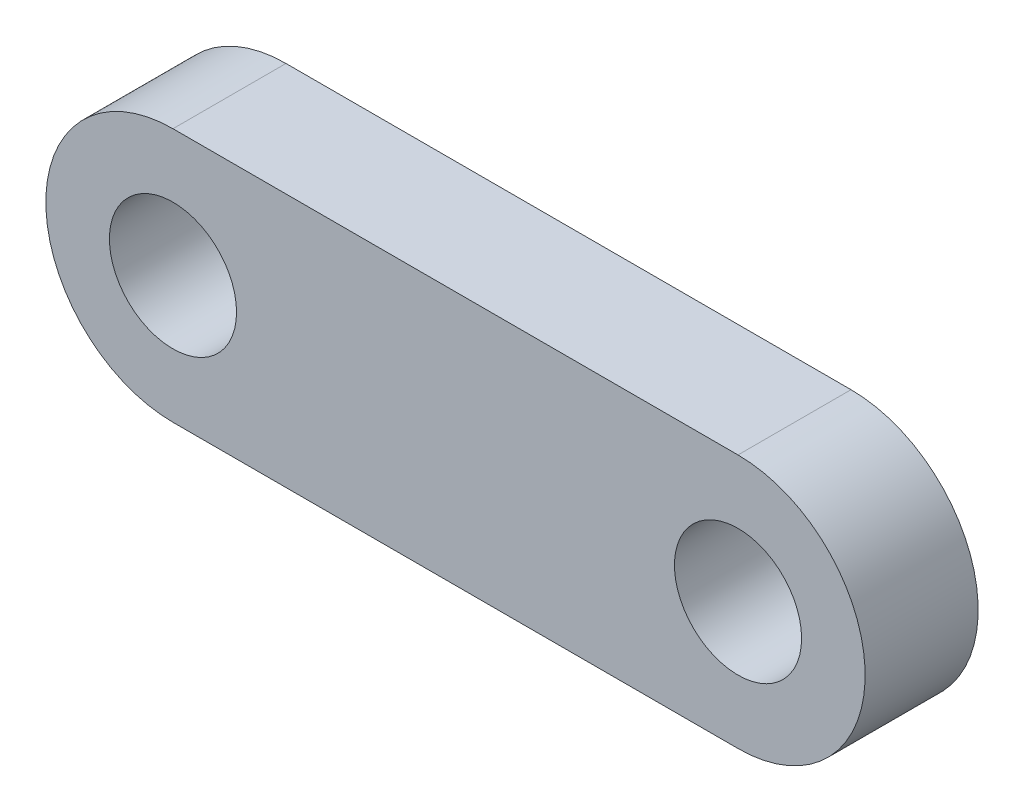
SolidWorks part; units mm, degrees
ref_plane "Front Plane" through (0, 0, 0) normal (0, 0, 1) x (1, 0, 0)
ref_plane "Top Plane" through (0, 0, 0) normal (0, 1, 0) x (1, 0, 0)
ref_plane "Right Plane" through (0, 0, 0) normal (1, 0, 0) x (0, 0, -1)
sketch "Sketch1" plane through (0, 0, 0) normal (0, 0, 1) x (1, 0, 0)
  line L0 (-10, 4.5) -> (10, 4.5)
  line L1 (10, -4.5) -> (-10, -4.5)
  circle A0 centre (-10, 0) radius 4.5
  circle A1 centre (10, 0) radius 4.5
  circle A2 centre (-10, 0) radius 2.25
  circle A3 centre (10, 0) radius 2.25
  dimension "D1" = 4.5
  dimension "D2" = 9
  dimension "D3" = 4.5
  dimension "D4" = 9
  dimension "D5" = 10
  dimension "D6" = 20
extrude "Boss-Extrude1" add sketch "Sketch1" along normal blind 4 contours A0 A2 | A1 L0 A0 L1 | A1 A3
